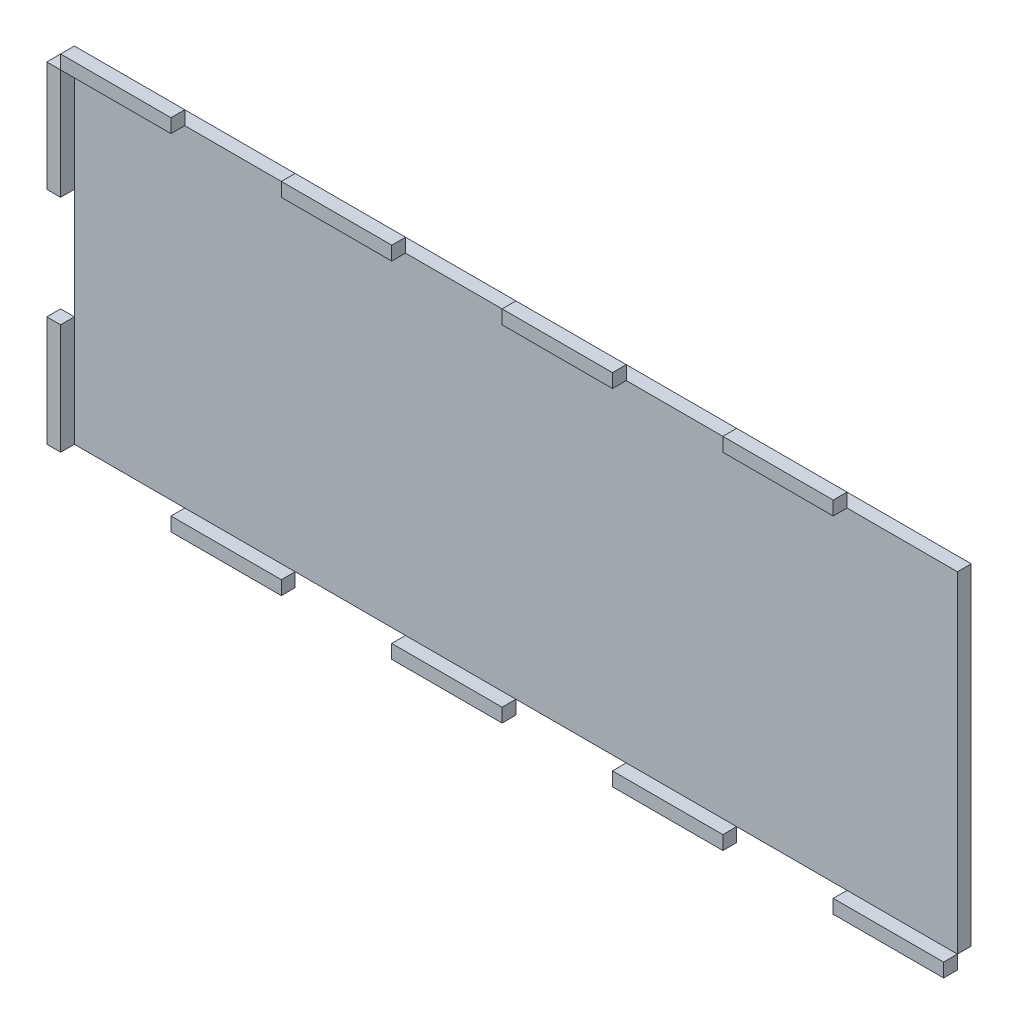
SolidWorks part; units mm, degrees
ref_plane "Front Plane" through (0, 0, 0) normal (0, 0, 1) x (1, 0, 0)
ref_plane "Top Plane" through (0, 0, 0) normal (0, 1, 0) x (1, 0, 0)
ref_plane "Right Plane" through (0, 0, 0) normal (1, 0, 0) x (0, 0, -1)
sketch "Sketch1" plane through (0, 0, 0) normal (0, 0, 1) x (1, 0, 0)
  line L1 (-101.6, -38.1) -> (101.6, -38.1)
  line L2 (-101.6, -38.1) -> (-101.6, 38.1)
  line L3 (-101.6, 38.1) -> (101.6, 38.1)
  line L4 (101.6, -38.1) -> (101.6, 38.1)
  line L5 (-101.6, -38.1) -> (101.6, 38.1) construction
  line L6 (-101.6, 38.1) -> (101.6, -38.1) construction
  point P0 (0, 0)
  dimension "D1" = 203.2
  dimension "D2" = 76.2
extrude "Boss-Extrude1" add sketch "Sketch1" along normal blind 3.175
sketch "Sketch2" plane through (0, 0, 3.175) normal (0, 0, 1) x (1, 0, 0)
  line L0 (-50.8, 38.1) -> (-50.8, 41.275)
  line L1 (-101.6, 38.1) -> (-76.2, 38.1)
  line L2 (-101.6, 38.1) -> (-101.6, 41.275)
  line L3 (-101.6, 41.275) -> (-76.2, 41.275)
  line L4 (-76.2, 38.1) -> (-76.2, 41.275)
  line L5 (-50.8, 38.1) -> (-25.4, 38.1)
  line L6 (-25.4, 38.1) -> (-25.4, 41.275)
  line L7 (-50.8, 41.275) -> (-25.4, 41.275)
  line L8 (0, 38.1) -> (0, 41.275)
  line L9 (0, 38.1) -> (25.4, 38.1)
  line L10 (25.4, 38.1) -> (25.4, 41.275)
  line L11 (0, 41.275) -> (25.4, 41.275)
  line L12 (50.8, 38.1) -> (50.8, 41.275)
  line L13 (50.8, 38.1) -> (76.2, 38.1)
  line L14 (76.2, 38.1) -> (76.2, 41.275)
  line L15 (50.8, 41.275) -> (76.2, 41.275)
  point P5 (-76.2, 39.6875)
  dimension "D1" = 25.4
  dimension "D2" = 3.175
  dimension "D3" = 4
extrude "Boss-Extrude2" add sketch "Sketch2" along normal blind 3.175 separate body
sketch "Sketch3" plane through (0, 0, 3.175) normal (0, 0, 1) x (1, 0, 0)
  line L0 (50.8, -38.1) -> (50.8, -41.275)
  line L1 (101.6, -38.1) -> (76.2, -38.1)
  line L2 (101.6, -38.1) -> (101.6, -41.275)
  line L3 (101.6, -41.275) -> (76.2, -41.275)
  line L4 (76.2, -38.1) -> (76.2, -41.275)
  line L5 (50.8, -38.1) -> (25.4, -38.1)
  line L6 (25.4, -38.1) -> (25.4, -41.275)
  line L7 (50.8, -41.275) -> (25.4, -41.275)
  line L8 (0, -38.1) -> (0, -41.275)
  line L9 (0, -38.1) -> (-25.4, -38.1)
  line L10 (-25.4, -38.1) -> (-25.4, -41.275)
  line L11 (0, -41.275) -> (-25.4, -41.275)
  line L12 (-50.8, -38.1) -> (-50.8, -41.275)
  line L13 (-50.8, -38.1) -> (-76.2, -38.1)
  line L14 (-76.2, -38.1) -> (-76.2, -41.275)
  line L15 (-50.8, -41.275) -> (-76.2, -41.275)
  dimension "D1" = 25.4
  dimension "D2" = 3.175
  dimension "D3" = 4
extrude "Boss-Extrude3" add sketch "Sketch3" along normal blind 3.175 separate body
sketch "Sketch4" plane through (0, 0, 3.175) normal (0, 0, 1) x (1, 0, 0)
  line L1 (-101.6, -38.1) -> (-104.775, -38.1)
  line L2 (-101.6, -38.1) -> (-101.6, -12.7)
  line L3 (-101.6, -12.7) -> (-104.775, -12.7)
  line L4 (-104.775, -38.1) -> (-104.775, -12.7)
  line L5 (-101.6, 38.1) -> (-104.775, 38.1)
  line L6 (-101.6, 38.1) -> (-101.6, 12.7)
  line L7 (-101.6, 12.7) -> (-104.775, 12.7)
  line L8 (-104.775, 38.1) -> (-104.775, 12.7)
  dimension "D1" = 25.4
  dimension "D2" = 3.175
  dimension "D3" = 25.4
extrude "Boss-Extrude4" add sketch "Sketch4" along normal blind 3.175 separate body
sketch "Sketch5" plane through (0, 0, 3.175) normal (0, 0, 1) x (1, 0, 0)
  line L0 (101.6, -38.1) -> (101.6, 38.1) construction
  line L1 (101.6, 12.7) -> (104.775, 12.7)
  line L2 (101.6, 12.7) -> (101.6, -12.7)
  line L3 (101.6, -12.7) -> (104.775, -12.7)
  line L4 (104.775, 12.7) -> (104.775, -12.7)
  line L6 (101.6, -38.1) -> (76.2, -38.1) construction
  point P6 (103.1875, -12.7)
  point P8 (102.6198, -16.7012)
  point P9 (0, 0)
  dimension "D1" = 3.175
  dimension "D2" = 25.4
  dimension "D3" = 25.4
